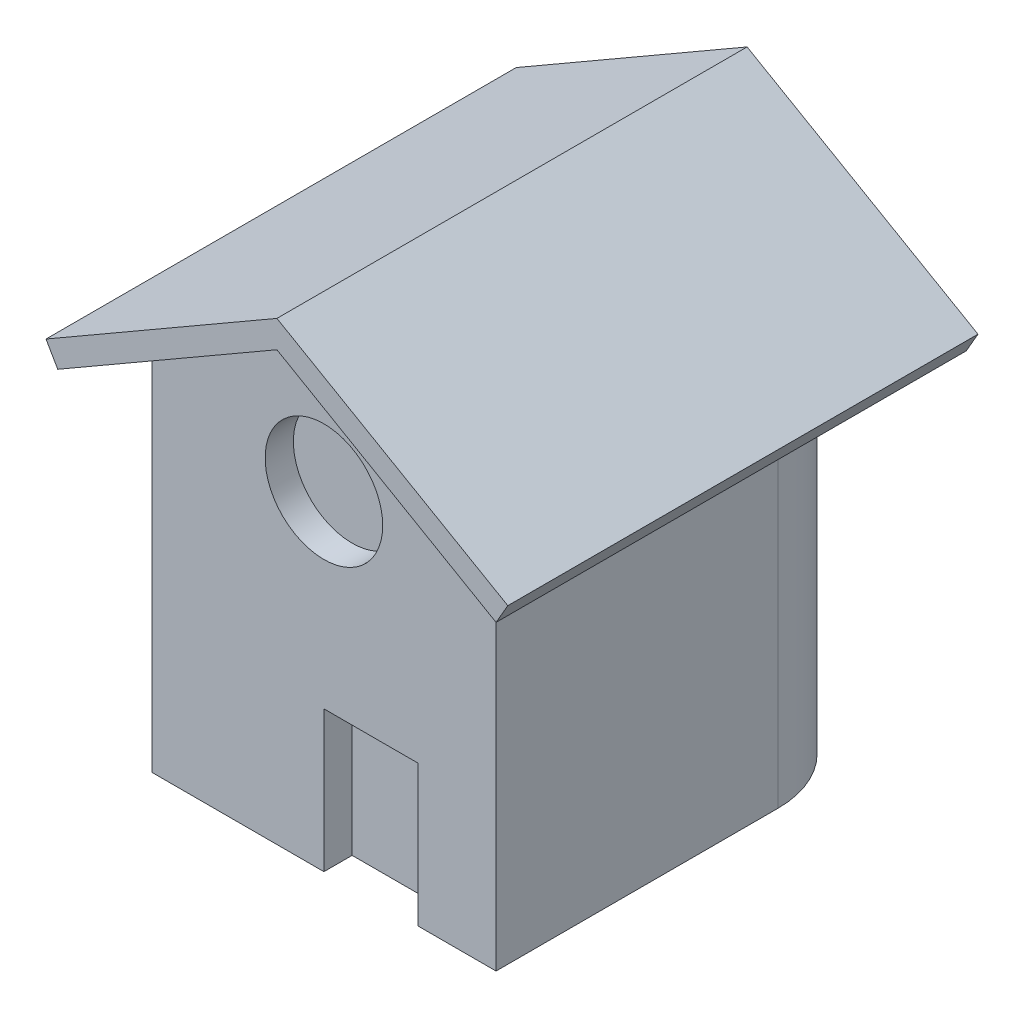
SolidWorks part; units mm, degrees
ref_plane "Front Plane" through (0, 0, 0) normal (0, 0, 1) x (1, 0, 0)
ref_plane "Top Plane" through (0, 0, 0) normal (0, 1, 0) x (1, 0, 0)
ref_plane "Right Plane" through (0, 0, 0) normal (1, 0, 0) x (0, 0, -1)
sketch "Sketch1" plane through (0, 0, 0) normal (0, 0, 1) x (1, 0, 0)
  line L0 (-18.305, 0) -> (18.305, 0)
  line L1 (18.305, 0) -> (18.305, 40)
  line L2 (18.305, 40) -> (0, 50.5684)
  line L3 (0, 50.5684) -> (-18.305, 40)
  line L4 (-18.305, 40) -> (-18.305, 0)
  dimension "D1" = 36.61
  dimension "D2" = 40
  dimension "D3" = 240
extrude "Boss-Extrude1" add sketch "Sketch1" along normal mid plane 40
sketch "Sketch2" plane through (0, 0, 20) normal (0, 0, 1) x (1, 0, 0)
  line L0 (-18.305, 0) -> (18.305, 0) construction
  line L1 (10, 0) -> (0, 0)
  line L2 (10, 0) -> (10, 15)
  line L3 (10, 15) -> (0, 15)
  line L4 (0, 0) -> (0, 15)
  circle A0 centre (0, 35) radius 6.25
  point P8 (0, 0)
  point P9 (0, 0)
  dimension "D3" = 12.5
  dimension "D1" = 10
  dimension "D2" = 15
  dimension "D4" = 35
extrude "Cut-Extrude1" cut sketch "Sketch2" against normal blind 3
fillet "Fillet2" radius 10 2 edges at (-18.305, 20, -20) (18.305, 20, -20)
sketch "Sketch3" plane through (0, 0, 0) normal (0, 0, 1) x (1, 0, 0)
  line L0 (0, 50.5684) -> (23.305, 37.1132)
  line L1 (23.305, 37.1132) -> (24.555, 39.2783)
  line L2 (24.555, 39.2783) -> (0, 53.4551)
  line L3 (0, 53.4551) -> (-24.555, 39.2783)
  line L4 (-24.555, 39.2783) -> (-23.305, 37.1132)
  line L5 (-23.305, 37.1132) -> (0, 50.5684)
  line L6 (0, 50.5684) -> (-18.305, 40) construction
  line L7 (18.305, 40) -> (0, 50.5684) construction
  line L8 (-18.305, 40) -> (-18.305, 0) construction
  dimension "D1" = 2.5
  dimension "D2" = 5
extrude "Boss-Extrude2" add sketch "Sketch3" along normal mid plane 50
